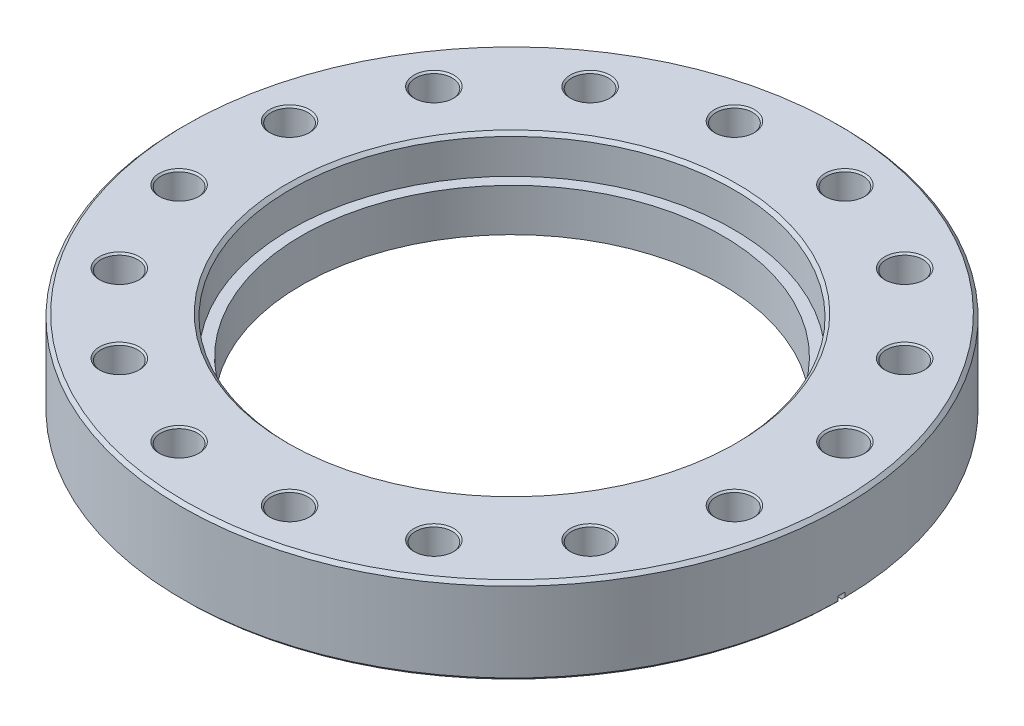
SolidWorks part; units mm, degrees
ref_plane "Front Plane" through (0, 0, 0) normal (0, 0, 1) x (1, 0, 0)
ref_plane "Top Plane" through (0, 0, 0) normal (0, 1, 0) x (1, 0, 0)
ref_plane "Right Plane" through (0, 0, 0) normal (1, 0, 0) x (0, 0, -1)
sketch "Sketch1" plane through (0, 0, 0) normal (0, 1, 0) x (1, 0, 0)
  circle A0 centre (0, 0) radius 75.819
  circle A1 centre (0, 0) radius 48.387
  dimension "D1" = 151.638
  dimension "D2" = 96.774
extrude "Boss-Extrude1" add sketch "Sketch1" along normal blind 19.812
sketch "Sketch2" plane through (0, 19.812, 0) normal (0, 1, 0) x (1, 0, 0)
  circle A0 centre (0, 0) radius 50.927
  dimension "D1" = 101.854
extrude "Cut-Extrude1" cut sketch "Sketch2" against normal blind 8.7122
chamfer "Chamfer1" distance 0.762 angle 45 3 edges at (0, 0, 75.819) (0, 19.812, 75.819) (0, 19.812, 50.927)
sketch "Sketch3" plane through (0, 0, 0) normal (0, 0, 1) x (1, 0, 0)
  line L0 (-60.325, 0) -> (-60.325, 1.6256)
  line L1 (-60.325, 1.6256) -> (-57.658, 0.6604)
  line L2 (-57.658, 0.6604) -> (-57.658, 1.27)
  line L3 (-57.658, 1.27) -> (0, 1.27)
  line L4 (-60.325, 0) -> (0, 0)
  line L5 (0, 0) -> (0, 1.27)
  line L6 (-75.057, 0) -> (75.057, 0) construction
  dimension "D1" = 60.325
  dimension "D2" = 57.658
  dimension "D3" = 1.6256
  dimension "D4" = 0.6096
  dimension "D5" = 1.27
revolve "Cut-Revolve1" cut sketch "Sketch3" angle 360 about axis through (0, 19.812, 0) along (0, -1, 0)
sketch "Sketch4" plane through (0, 19.812, 0) normal (0, 1, 0) x (1, 0, 0)
  line L0 (0, 48.387) -> (0, 0) construction
  line L1 (0, 0) -> (-12.7054, 63.8742) construction
  circle A0 centre (-12.7054, 63.8742) radius 4.2164
  circle A1 centre (0, 0) radius 48.387 construction
  dimension "D1" = 8.4328
  dimension "D2" = 65.1256
  dimension "D3" = 11.25
extrude "Cut-Extrude2" cut sketch "Sketch4" against normal through all
chamfer "Chamfer2" distance 0.381 angle 45 2 edges at (-12.7054, 19.812, -59.6578) (-12.7054, 0, -59.6578)
pattern_circular "CirPattern1" count 16 every 22.5 about axis through (0, 0, 0) along (0, 1, 0) of "Cut-Extrude2", "Chamfer2"
sketch "Sketch5" plane through (0, 0, 0) normal (0, 0, 1) x (1, 0, 0)
  line L0 (-59.3102, 0.9132) -> (-75.819, 1.7784)
  line L1 (0, -2.1951) -> (0, 0) construction
  line L2 (-75.819, 1.7784) -> (-75.819, -2.1951)
  line L3 (-75.819, -2.1951) -> (-59.3102, -2.1951)
  line L4 (59.3102, 0.9132) -> (59.3102, -2.1951)
  line L5 (75.819, -2.1951) -> (59.3102, -2.1951)
  line L6 (75.819, 1.7784) -> (75.819, -2.1951)
  line L7 (-59.3102, 0.9132) -> (-59.3102, -2.1951)
  line L8 (59.3102, 0.9132) -> (75.819, 1.7784)
  line L9 (0, -2.1951) -> (-59.3102, -2.1951) construction
  line L10 (0, -2.1951) -> (-59.3102, 0.9132) construction
  dimension "D1" = 2.1951
  dimension "D3" = 3
extrude "Cut-Extrude3" cut sketch "Sketch5" against normal mid plane 1.5875
